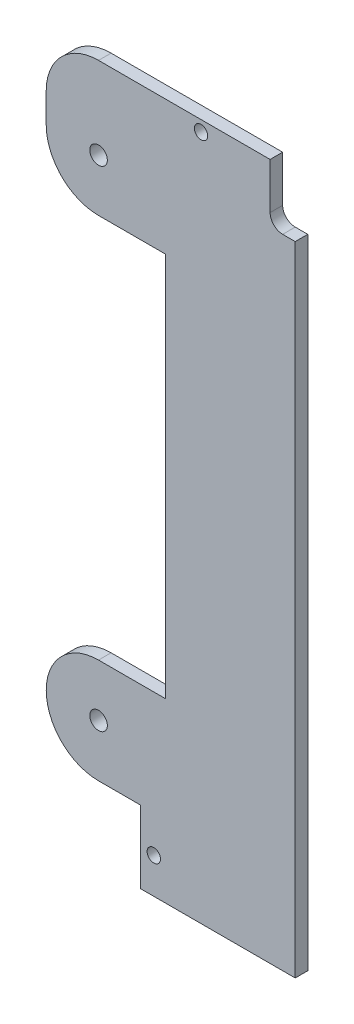
SolidWorks part; units mm, degrees
material "6061-T6 Black anodised"
ref_plane "Front Plane" through (0, 0, 0) normal (0, 0, 1) x (1, 0, 0)
ref_plane "Top Plane" through (0, 0, 0) normal (0, 1, 0) x (1, 0, 0)
ref_plane "Right Plane" through (0, 0, 0) normal (1, 0, 0) x (0, 0, -1)
sketch "Sketch1" plane through (0, 0, 0) normal (0, 0, 1) x (1, 0, 0)
  line L0 (41, 136.6) -> (41, 125.6)
  line L1 (0, 136.6) -> (41, 136.6)
  line L2 (-12.5, 124.1) -> (-12.5, 117)
  line L3 (10, -29.8) -> (47, -29.8)
  line L4 (47, 122.6) -> (47, -29.8)
  line L5 (44, 122.6) -> (47, 122.6)
  line L6 (16, 104.5) -> (16, 12.5)
  line L7 (0, 12.5) -> (16, 12.5)
  line L8 (0, 104.5) -> (16, 104.5)
  line L10 (10, -29.8) -> (10, -12.5)
  line L11 (0, -12.5) -> (10, -12.5)
  circle A0 centre (0, 0) radius 2.1
  circle A1 centre (0, 117) radius 2.1
  circle A2 centre (13.2, -21.3) radius 1.6
  circle A3 centre (24.5, 134) radius 1.6
  arc A4 (41, 125.6) -> (44, 122.6) centre (44, 125.6) ccw
  arc A5 (0, 12.5) -> (0, -12.5) centre (0, 0) ccw
  arc A6 (-12.5, 117) -> (0, 104.5) centre (0, 117) ccw
  arc A7 (0, 136.6) -> (-12.5, 124.1) centre (0, 124.1) ccw
  dimension "D8" = 3.2
  dimension "D9" = 3
  dimension "D13" = 21.3
  dimension "D16" = 3.2
  dimension "D17" = 4.2
  dimension "D1" = 12.5
  dimension "D2" = 117
  dimension "D3" = 29.8
  dimension "D4" = 166.4
  dimension "D5" = 47
  dimension "D6" = 24.5
  dimension "D7" = 17
  dimension "D10" = 14
  dimension "D11" = 6
  dimension "D12" = 13.2
  dimension "D14" = 28.5
  dimension "D15" = 22.5
extrude "Boss-Extrude1" add sketch "Sketch1" along normal blind 3
